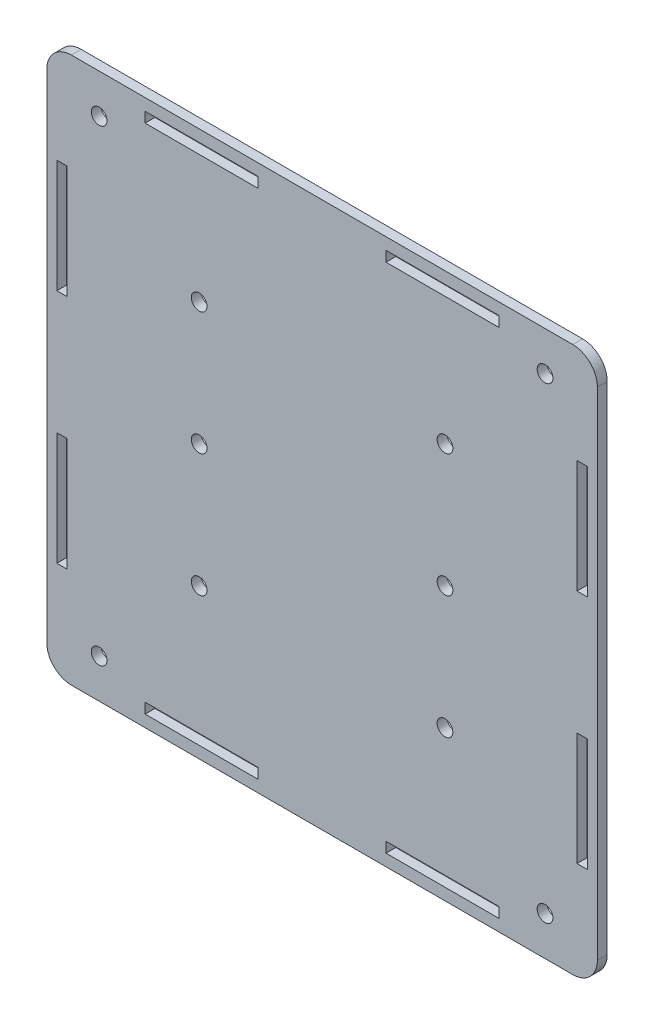
SolidWorks part; units mm, degrees
ref_plane "前视基准面" through (0, 0, 0) normal (0, 0, 1) x (1, 0, 0)
ref_plane "上视基准面" through (0, 0, 0) normal (0, 1, 0) x (1, 0, 0)
ref_plane "右视基准面" through (0, 0, 0) normal (1, 0, 0) x (0, 0, -1)
sketch "草图1" plane through (0, 0, 0) normal (0, 0, 1) x (1, 0, 0)
  line L1 (-56, 55.5) -> (56, 55.5)
  line L2 (-56, 55.5) -> (-56, -55.5)
  line L3 (-56, -55.5) -> (56, -55.5)
  line L4 (56, 55.5) -> (56, -55.5)
  line L5 (-56, 55.5) -> (56, -55.5) construction
  line L6 (-56, -55.5) -> (56, 55.5) construction
  point P0 (0, 0)
  dimension "D1" = 111
  dimension "D2" = 112
extrude "凸台-拉伸1" add sketch "草图1" along normal blind 2
sketch "草图2" plane through (0, 0, 0) normal (0, 0, -1) x (-1, 0, 0)
  circle A0 centre (-45.35, -47.55) radius 1.6
  circle A1 centre (45.35, -47.55) radius 1.6
  circle A2 centre (45.35, 47.55) radius 1.6
  circle A3 centre (-45.35, 47.55) radius 1.6
  dimension "D2" = 3.2
  dimension "D1" = 45.35
  dimension "D3" = 47.55
  dimension "D4" = 2
  dimension "D5" = 2
extrude "切除-拉伸1" cut sketch "草图2" against normal through all
sketch "草图3" plane through (0, 0, 0) normal (0, 0, -1) x (-1, 0, 0)
  line L0 (0, 0) -> (0, -29.5446) construction
  line L1 (0, 0) -> (30.314, 0) construction
  line L3 (-53.95, 35.5) -> (-51.85, 35.5)
  line L4 (-53.95, 35.5) -> (-53.95, 12.5)
  line L5 (-53.95, 12.5) -> (-51.85, 12.5)
  line L6 (-51.85, 35.5) -> (-51.85, 12.5)
  line L7 (-53.95, -12.5) -> (-51.85, -12.5)
  line L8 (-53.95, -12.5) -> (-53.95, -35.5)
  line L9 (-53.95, -35.5) -> (-51.85, -35.5)
  line L10 (-51.85, -12.5) -> (-51.85, -35.5)
  line L11 (56, -55.5) -> (-56, -55.5) construction
  line L12 (-56, 55.5) -> (56, 55.5) construction
  line L13 (51.85, -12.5) -> (51.85, -35.5)
  line L14 (53.95, -35.5) -> (51.85, -35.5)
  line L15 (53.95, -12.5) -> (53.95, -35.5)
  line L16 (53.95, -12.5) -> (51.85, -12.5)
  line L17 (51.85, 35.5) -> (51.85, 12.5)
  line L18 (53.95, 12.5) -> (51.85, 12.5)
  line L19 (53.95, 35.5) -> (53.95, 12.5)
  line L20 (53.95, 35.5) -> (51.85, 35.5)
  line L21 (-56, -55.5) -> (-56, 55.5) construction
  line L22 (-36, -51) -> (-13, -51)
  line L23 (-36, -51) -> (-36, -53.1)
  line L24 (-36, -53.1) -> (-13, -53.1)
  line L25 (-13, -51) -> (-13, -53.1)
  line L26 (13, -51) -> (36, -51)
  line L27 (13, -51) -> (13, -53.1)
  line L28 (13, -53.1) -> (36, -53.1)
  line L29 (36, -51) -> (36, -53.1)
  line L30 (56, 55.5) -> (56, -55.5) construction
  line L31 (36, 51) -> (36, 53.1)
  line L32 (13, 53.1) -> (36, 53.1)
  line L33 (13, 51) -> (13, 53.1)
  line L34 (13, 51) -> (36, 51)
  line L35 (-13, 51) -> (-13, 53.1)
  line L36 (-36, 53.1) -> (-13, 53.1)
  line L37 (-36, 51) -> (-36, 53.1)
  line L38 (-36, 51) -> (-13, 51)
  point P16 (-52.9, 35.5)
  dimension "D1" = 2.1
  dimension "D2" = 2.1
  dimension "D3" = 51.85
  dimension "D4" = 23
  dimension "D5" = 23
  dimension "D6" = 20
  dimension "D7" = 20
  dimension "D8" = 51
  dimension "D9" = 2.1
  dimension "D10" = 2.1
  dimension "D11" = 23
  dimension "D12" = 23
  dimension "D13" = 20
  dimension "D14" = 20
extrude "切除-拉伸2" cut sketch "草图3" against normal through all
sketch "草图4" plane through (0, 0, 0) normal (0, 0, -1) x (-1, 0, 0)
  circle A0 centre (-25, -25) radius 1.6
  circle A1 centre (25, -25) radius 1.6
  circle A2 centre (25, 0) radius 1.6
  circle A3 centre (25, 25) radius 1.6
  circle A4 centre (-25, 0) radius 1.6
  circle A5 centre (-25, 25) radius 1.6
  dimension "D3" = 3.2
  dimension "D1" = 25
  dimension "D2" = 25
  dimension "D4" = 2
  dimension "D5" = 3
extrude "切除-拉伸3" cut sketch "草图4" against normal through all
fillet "圆角1" radius 5 4 edges at (56, -55.5, 1) (-56, -55.5, 1) (-56, 55.5, 1) (56, 55.5, 1)
